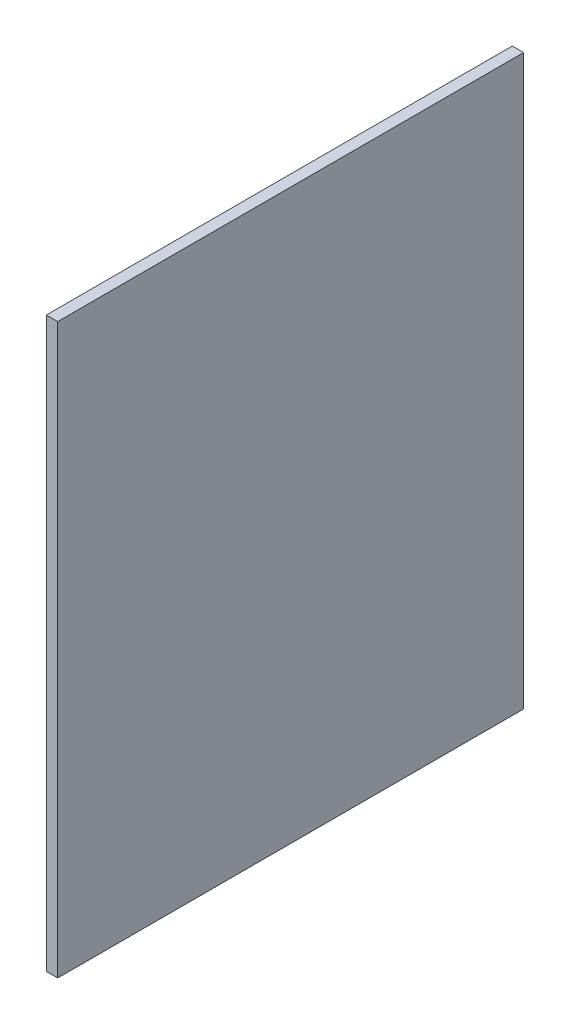
SolidWorks part; units mm, degrees
ref_plane "Front Plane" through (0, 0, 0) normal (0, 0, 1) x (1, 0, 0)
ref_plane "Top Plane" through (0, 0, 0) normal (0, 1, 0) x (1, 0, 0)
ref_plane "Right Plane" through (0, 0, 0) normal (1, 0, 0) x (0, 0, -1)
sketch "Sketch1" plane through (0, 0, 0) normal (1, 0, 0) x (0, 0, -1)
  line L1 (0, 0) -> (359, 0)
  line L2 (0, 0) -> (0, 438)
  line L3 (0, 438) -> (359, 438)
  line L4 (359, 0) -> (359, 438)
  dimension "D1" = 359
  dimension "D2" = 438
extrude "Boss-Extrude1" add sketch "Sketch1" along normal blind 8.75
